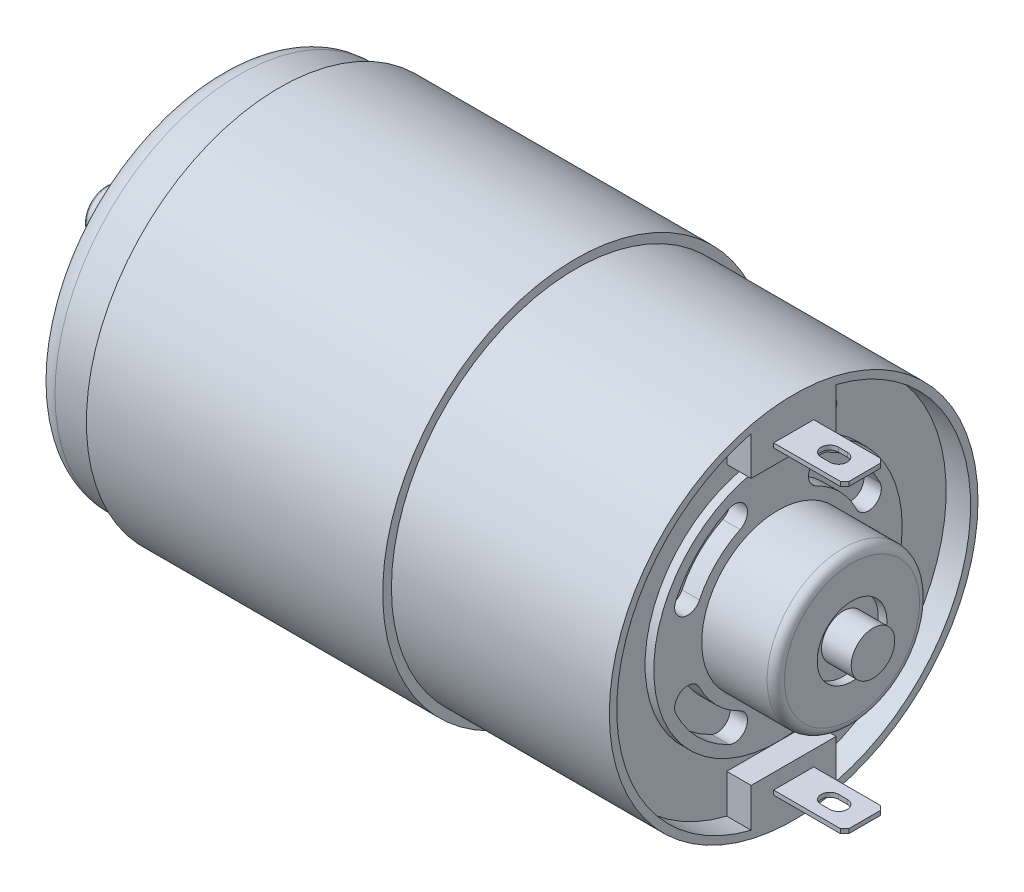
SolidWorks part; units mm, degrees
ref_plane "Front Plane" through (0, 0, 0) normal (0, 0, 1) x (1, 0, 0)
ref_plane "Top Plane" through (0, 0, 0) normal (0, 1, 0) x (1, 0, 0)
ref_plane "Right Plane" through (0, 0, 0) normal (1, 0, 0) x (0, 0, -1)
sketch "Sketch1" plane through (0, 0, 0) normal (0, 0, 1) x (1, 0, 0)
  line L0 (7.1, 22.15) -> (7.1, 0)
  line L1 (7.1, 0) -> (41.1, 0)
  line L2 (41.1, 0) -> (41.1, 22.15)
  line L3 (41.1, 22.15) -> (7.1, 22.15)
  line L4 (7.1, 0) -> (41.1, 0) construction
revolve "Revolve1" add sketch "Sketch1" angle 360 about L4
sketch "Sketch2" plane through (41.1, 0, 0) normal (1, 0, 0) x (0, 0, -1)
  circle A0 centre (0, 0) radius 21.15
extrude "Boss-Extrude1" add sketch "Sketch2" along normal blind 25
sketch "Sketch3" plane through (66.1, 0, 0) normal (1, 0, 0) x (0, 0, -1)
  line L0 (-2.3, 17) -> (-2.3, 17.5)
  line L1 (-2.3, 17.5) -> (2.3, 17.5)
  line L2 (2.3, 17.5) -> (2.3, 17)
  line L3 (2.3, 17) -> (-2.3, 17)
extrude "Boss-Extrude2" add sketch "Sketch3" along normal blind 8.15
sketch "Sketch4" plane through (0, 17.5, 0) normal (0, 1, 0) x (-1, 0, 0)
  line L0 (-71.25, -1) -> (-70.25, -1)
  line L1 (-70.25, 1) -> (-71.25, 1)
  arc A0 (-70.25, -1) -> (-70.25, 1) centre (-70.25, 0) ccw
  arc A1 (-71.25, 1) -> (-71.25, -1) centre (-71.25, 0) ccw
extrude "Cut-Extrude1" cut sketch "Sketch4" against normal through all
sketch "Sketch5" plane through (66.1, 0, 0) normal (1, 0, 0) x (0, 0, -1)
  line L0 (-2.3, -17.5) -> (-2.3, -17)
  line L1 (-2.3, -17) -> (2.3, -17)
  line L2 (2.3, -17) -> (2.3, -17.5)
  line L3 (2.3, -17.5) -> (-2.3, -17.5)
extrude "Boss-Extrude3" add sketch "Sketch5" along normal blind 8.15
sketch "Sketch6" plane through (0, -17.5, 0) normal (0, -1, 0) x (1, 0, 0)
  line L0 (71.25, 1) -> (70.25, 1)
  line L1 (70.25, -1) -> (71.25, -1)
  arc A0 (70.25, 1) -> (70.25, -1) centre (70.25, 0) ccw
  arc A1 (71.25, -1) -> (71.25, 1) centre (71.25, 0) ccw
extrude "Cut-Extrude2" cut sketch "Sketch6" against normal up to next
sketch "Sketch7" plane through (66.1, 0, 0) normal (1, 0, 0) x (0, 0, -1)
  line L0 (2.0689, 14.25) -> (2.0689, 15.25)
  line L1 (2.0689, 15.25) -> (-4.875, 15.25)
  line L2 (-4.875, 15.25) -> (-4.875, 19.7059)
  line L3 (-4.875, -19.7059) -> (-4.875, -15.25)
  line L4 (-4.875, -15.25) -> (4.875, -15.25)
  line L5 (4.875, -15.25) -> (4.875, -19.7059)
  line L6 (4.875, 19.7059) -> (4.875, 14.25)
  line L7 (4.875, 14.25) -> (2.0689, 14.25)
  arc A0 (-4.875, 19.7059) -> (-4.875, -19.7059) centre (0, 0) ccw
  arc A1 (4.875, -19.7059) -> (4.875, 19.7059) centre (0, 0) ccw
extrude "Cut-Extrude3" cut sketch "Sketch7" against normal blind 2.8
sketch "Sketch8" plane through (63.3, 0, 0) normal (1, 0, 0) x (0, 0, -1)
  circle A0 centre (0, 0) radius 14.25
extrude "Boss-Extrude4" add sketch "Sketch8" along normal blind 1
sketch "Sketch9" plane through (64.3, 0, 0) normal (1, 0, 0) x (0, 0, -1)
  arc A0 (-5.6522, 11.707) -> (-11.707, 5.6522) centre (0, 0) ccw
  arc A1 (-11.707, 5.6522) -> (-9.0054, 4.3478) centre (-10.3562, 5) ccw
  arc A2 (-9.0054, 4.3478) -> (-4.3478, 9.0054) centre (0, 0) cw
  arc A3 (-4.3478, 9.0054) -> (-5.6522, 11.707) centre (-5, 10.3562) ccw
extrude "Cut-Extrude4" cut sketch "Sketch9" against normal blind 2
sketch "Sketch10" plane through (64.3, 0, 0) normal (1, 0, 0) x (0, 0, -1)
  arc A0 (11.707, 5.6522) -> (5.6522, 11.707) centre (0, 0) ccw
  arc A1 (5.6522, 11.707) -> (4.3478, 9.0054) centre (5, 10.3562) ccw
  arc A2 (4.3478, 9.0054) -> (9.0054, 4.3478) centre (0, 0) cw
  arc A3 (9.0054, 4.3478) -> (11.707, 5.6522) centre (10.3562, 5) ccw
extrude "Cut-Extrude5" cut sketch "Sketch10" against normal blind 2
sketch "Sketch11" plane through (64.3, 0, 0) normal (1, 0, 0) x (0, 0, -1)
  arc A0 (5.6522, -11.707) -> (11.707, -5.6522) centre (0, 0) ccw
  arc A1 (11.707, -5.6522) -> (9.0054, -4.3478) centre (10.3562, -5) ccw
  arc A2 (9.0054, -4.3478) -> (4.3478, -9.0054) centre (0, 0) cw
  arc A3 (4.3478, -9.0054) -> (5.6522, -11.707) centre (5, -10.3562) ccw
extrude "Cut-Extrude6" cut sketch "Sketch11" against normal blind 2
sketch "Sketch12" plane through (64.3, 0, 0) normal (1, 0, 0) x (0, 0, -1)
  arc A0 (-11.707, -5.6522) -> (-5.6522, -11.707) centre (0, 0) ccw
  arc A1 (-5.6522, -11.707) -> (-4.3478, -9.0054) centre (-5, -10.3562) ccw
  arc A2 (-4.3478, -9.0054) -> (-9.0054, -4.3478) centre (0, 0) cw
  arc A3 (-9.0054, -4.3478) -> (-11.707, -5.6522) centre (-10.3562, -5) ccw
extrude "Cut-Extrude7" cut sketch "Sketch12" against normal blind 2
sketch "Sketch13" plane through (7.1, 0, 0) normal (-1, 0, 0) x (0, 0, 1)
  circle A0 centre (0, 0) radius 21.15
extrude "Boss-Extrude5" add sketch "Sketch13" along normal blind 7.1
sketch "Sketch14" plane through (0, 0, 0) normal (-1, 0, 0) x (0, 0, 1)
  line L0 (6.7619, 14.5009) -> (4.7756, 10.2413)
  line L1 (10.2413, 4.7756) -> (14.5009, 6.7619)
  arc A0 (14.5009, 6.7619) -> (6.7619, 14.5009) centre (0, 0) ccw
  arc A1 (4.7756, 10.2413) -> (10.2413, 4.7756) centre (0, 0) cw
extrude "Cut-Extrude8" cut sketch "Sketch14" against normal blind 10
sketch "Sketch15" plane through (0, 0, 0) normal (-1, 0, 0) x (0, 0, 1)
  line L0 (-6.7619, -14.5009) -> (-4.7756, -10.2413)
  line L1 (-10.2413, -4.7756) -> (-14.5009, -6.7619)
  arc A0 (-14.5009, -6.7619) -> (-6.7619, -14.5009) centre (0, 0) ccw
  arc A1 (-4.7756, -10.2413) -> (-10.2413, -4.7756) centre (0, 0) cw
extrude "Cut-Extrude9" cut sketch "Sketch15" against normal blind 10
sketch "Sketch16" plane through (0, 0, 0) normal (-1, 0, 0) x (0, 0, 1)
  line L0 (-14.5009, 6.7619) -> (-10.2413, 4.7756)
  line L1 (-4.7756, 10.2413) -> (-6.7619, 14.5009)
  arc A0 (-6.7619, 14.5009) -> (-14.5009, 6.7619) centre (0, 0) ccw
  arc A1 (-10.2413, 4.7756) -> (-4.7756, 10.2413) centre (0, 0) cw
extrude "Cut-Extrude10" cut sketch "Sketch16" against normal blind 10
sketch "Sketch17" plane through (0, 0, 0) normal (-1, 0, 0) x (0, 0, 1)
  line L0 (14.5009, -6.7619) -> (10.2413, -4.7756)
  line L1 (4.7756, -10.2413) -> (6.7619, -14.5009)
  arc A0 (6.7619, -14.5009) -> (14.5009, -6.7619) centre (0, 0) ccw
  arc A1 (10.2413, -4.7756) -> (4.7756, -10.2413) centre (0, 0) cw
extrude "Cut-Extrude11" cut sketch "Sketch17" against normal blind 10
sketch "Sketch18" plane through (64.3, 0, 0) normal (1, 0, 0) x (0, 0, -1)
  circle A0 centre (0, 0) radius 8.75
extrude "Boss-Extrude6" add sketch "Sketch18" along normal blind 8.5
hole_wizard "Hole1" positions "Sketch20" profile "Sketch19" legacy
sketch "Sketch20" plane through (72.8, 0, 0) normal (1, 0, 0) x (0, 0, -1)
  point P0 (0, 0)
sketch "Sketch19" plane through (72.8, 0, 0) normal (0, 1, 0) x (0, 0, -1)
  line L0 (0, 0) -> (0, 1)
  line L1 (0, 1) -> (4, 1)
  line L2 (4, 1) -> (4, 0)
  line L3 (4, 0) -> (0, 0)
  line L4 (0, 110) -> (0, -10) construction
  dimension "Diameter" = 8
  dimension "Depth" = 1
sketch "Sketch21" plane through (0, 0, 0) normal (-1, 0, 0) x (0, 0, 1)
  circle A0 centre (0, 0) radius 8.9
extrude "Boss-Extrude7" add sketch "Sketch21" along normal blind 5
hole_wizard "1/2 Clearance Hole1" positions "Sketch23" profile "Sketch22" hole size "1/2" standard "ANSI Inch"
sketch "Sketch23" plane through (-5, 0, 0) normal (-1, 0, 0) x (0, 0, 1)
  point P0 (0, 0)
sketch "Sketch22" plane through (-5, 0, 0) normal (0, 1, 0) x (0, 0, 1)
  line L0 (0, 0) -> (0, 1)
  line L1 (0, 1) -> (6.625, 1)
  line L2 (6.625, 1) -> (6.625, 0)
  line L5 (6.625, 0) -> (0, 0)
  line L10 (0, 1) -> (-6.625, 1) construction
  line L11 (0, -6.35) -> (0, 107.95) construction
  dimension "Hole Dia." = 13.25
  dimension "Hole Depth" = 1
  dimension "Drill Angle" = 180
ref_plane "Plane1" through (0, 0, 0) normal (0, 0, -1) x (-1, 0, 0)
sketch "Sketch24" plane through (0, 0, 0) normal (0, 0, -1) x (-1, 0, 0)
  line L0 (4, 3.75) -> (4, 0)
  line L1 (4, 0) -> (12.8, 0)
  line L2 (12.8, 0) -> (12.8, 2.5)
  line L3 (12.8, 2.5) -> (5, 2.5)
  line L4 (5, 2.5) -> (5, 3.75)
  line L5 (5, 3.75) -> (4, 3.75)
  line L6 (4, 0) -> (12.8, 0) construction
revolve "Revolve2" add sketch "Sketch24" angle 360 about L6
sketch "Sketch25" plane through (0, 0, 0) normal (0, 0, -1) x (-1, 0, 0)
  line L0 (-75.2, 2.5) -> (-75.2, 0)
  line L1 (-75.2, 0) -> (-71.8, 0)
  line L2 (-71.8, 0) -> (-71.8, 2.5)
  line L3 (-71.8, 2.5) -> (-75.2, 2.5)
  line L4 (-75.2, 0) -> (-71.8, 0) construction
revolve "Revolve3" add sketch "Sketch25" angle 360 about L4
hole_wizard "#2 Clearance Hole1" positions "Sketch27" profile "Sketch26" hole size "#2" standard "ANSI Inch"
sketch "Sketch27" plane through (63.3, 0, 0) normal (1, 0, 0) x (0, 0, -1)
  point P0 (6.5, 15)
sketch "Sketch26" plane through (63.3, 15, -6.5) normal (0, 1, 0) x (0, 0, -1)
  line L0 (0, 0) -> (0, 0.1)
  line L1 (0, 0.1) -> (1.25, 0.1)
  line L2 (1.25, 0.1) -> (1.25, 0)
  line L5 (1.25, 0) -> (0, 0)
  line L10 (0, 0.1) -> (-1.25, 0.1) construction
  line L11 (0, -6.35) -> (0, 107.95) construction
  dimension "Hole Dia." = 2.5
  dimension "Hole Depth" = 0.1
  dimension "Drill Angle" = 180
hole_wizard "#4 Clearance Hole1" positions "Sketch29" profile "Sketch28" hole size "#4" standard "ANSI Inch"
sketch "Sketch29" plane through (0, 0, 0) normal (-1, 0, 0) x (0, 0, 1)
  point P0 (0, 14.5)
  point P1 (0, -14.5)
sketch "Sketch28" plane through (0, 14.5, 0) normal (0, 1, 0) x (0, 0, 1)
  line L0 (0, 0) -> (0, 12.4914)
  line L1 (0, 12.4914) -> (1.65, 11.5)
  line L2 (1.65, 11.5) -> (1.65, 0)
  line L5 (1.65, 0) -> (0, 0)
  line L10 (0, 12.4914) -> (-1.65, 11.5) construction
  line L11 (0, -6.35) -> (0, 107.95) construction
  dimension "Hole Dia." = 3.3
  dimension "Hole Depth" = 11.5
  dimension "Drill Angle" = 118
chamfer "Chamfer1" distance 0.5 angle 45 4 edges at (74.25, 17.25, 2.3) (74.25, -17.25, -2.3) (74.25, 17.25, -2.3) (74.25, -17.25, 2.3)
fillet "Fillet1" radius 0.25 1 edges at (-12.8, 0, 2.5)
fillet "Fillet2" radius 0.75 1 edges at (-5, 0, 8.9)
fillet "Fillet3" radius 1 1 edges at (72.8, 0, -8.75)
fillet "Fillet4" radius 2.5 1 edges at (0, 0, 21.15)
